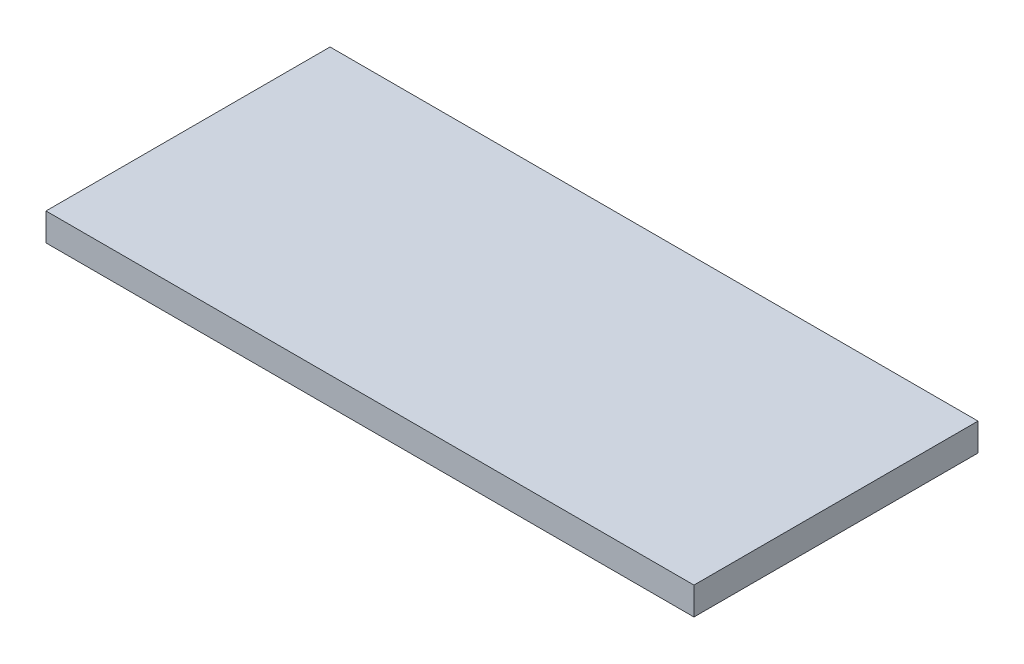
SolidWorks part; units mm, degrees
ref_plane "Front Plane" through (0, 0, 0) normal (0, 0, 1) x (1, 0, 0)
ref_plane "Top Plane" through (0, 0, 0) normal (0, 1, 0) x (1, 0, 0)
ref_plane "Right Plane" through (0, 0, 0) normal (1, 0, 0) x (0, 0, -1)
sketch "Sketch1" plane through (0, 0, 0) normal (0, 1, 0) x (1, 0, 0)
  line L1 (0, 0) -> (36.5, 0)
  line L2 (0, 0) -> (0, 16)
  line L3 (0, 16) -> (36.5, 16)
  line L4 (36.5, 0) -> (36.5, 16)
  dimension "D1" = 36.5
  dimension "D2" = 16
extrude "Boss-Extrude1" add sketch "Sketch1" along normal blind 1.56 contours L2 L3 L4 L1
